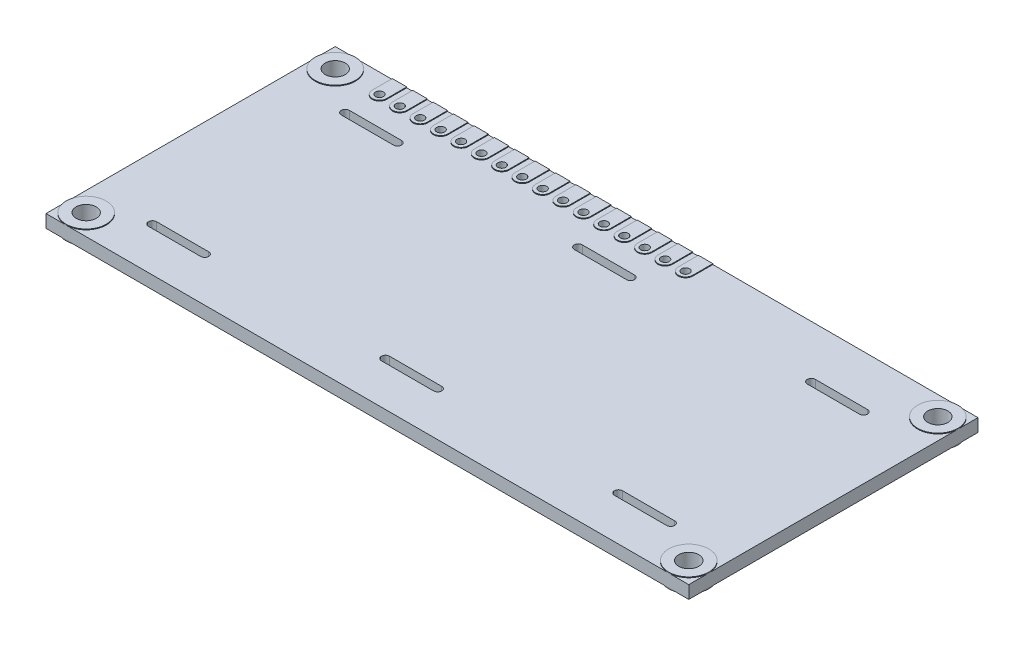
SolidWorks part; units mm, degrees
ref_plane "Front Plane" through (0, 0, 0) normal (0, 0, 1) x (1, 0, 0)
ref_plane "Top Plane" through (0, 0, 0) normal (0, 1, 0) x (1, 0, 0)
ref_plane "Right Plane" through (0, 0, 0) normal (1, 0, 0) x (0, 0, -1)
sketch "Sketch1" plane through (0, 0, 0) normal (0, 1, 0) x (1, 0, 0)
  line L0 (-32, 15.5) -> (-29.46, 15.5) construction
  line L1 (40, 18) -> (-40, 18)
  line L2 (40, 18) -> (40, -18)
  line L3 (40, -18) -> (-40, -18)
  line L4 (-40, 18) -> (-40, -18)
  line L5 (40, 18) -> (-40, -18) construction
  line L6 (40, -18) -> (-40, 18) construction
  line L7 (-37.5, 15.5) -> (37.5, 15.5) construction
  line L8 (-37.5, 15.5) -> (-37.5, -15.5) construction
  line L10 (37.5, 15.5) -> (37.5, -15.5) construction
  line L11 (-37.5, 15.5) -> (37.5, -15.5) construction
  line L12 (-37.5, -15.5) -> (37.5, 15.5) construction
  line L13 (0, 15.5) -> (0, -15.5) construction
  line L14 (-3.25, -12.5) -> (3.25, -12.5) construction
  line L15 (-3.25, -12) -> (3.25, -12)
  line L16 (-3.25, -13) -> (3.25, -13)
  line L17 (25.75, -12.5) -> (32.25, -12.5) construction
  line L18 (25.75, -12) -> (32.25, -12)
  line L19 (25.75, -13) -> (32.25, -13)
  line L20 (25.75, 11.5) -> (32.25, 11.5) construction
  line L21 (25.75, 12) -> (32.25, 12)
  line L22 (25.75, 11) -> (32.25, 11)
  line L23 (-3.25, 11.5) -> (3.25, 11.5) construction
  line L24 (-3.25, 12) -> (3.25, 12)
  line L25 (-3.25, 11) -> (3.25, 11)
  line L26 (-32.25, -12.5) -> (-25.75, -12.5) construction
  line L27 (-32.25, -12) -> (-25.75, -12)
  line L28 (-32.25, -13) -> (-25.75, -13)
  line L29 (-32.25, 11.5) -> (-25.75, 11.5) construction
  line L30 (-32.25, 12) -> (-25.75, 12)
  line L31 (-32.25, 11) -> (-25.75, 11)
  circle A0 centre (-37.5, 15.5) radius 1.25
  circle A1 centre (-37.5, -15.5) radius 1.25
  circle A2 centre (37.5, 15.5) radius 1.25
  circle A3 centre (37.5, -15.5) radius 1.25
  circle A4 centre (-32, 15.5) radius 0.5
  circle A5 centre (-29.46, 15.5) radius 0.5
  circle A6 centre (-26.92, 15.5) radius 0.5
  circle A7 centre (-24.38, 15.5) radius 0.5
  circle A8 centre (-21.84, 15.5) radius 0.5
  circle A9 centre (-19.3, 15.5) radius 0.5
  circle A10 centre (-16.76, 15.5) radius 0.5
  circle A11 centre (-14.22, 15.5) radius 0.5
  circle A12 centre (-11.68, 15.5) radius 0.5
  circle A13 centre (-9.14, 15.5) radius 0.5
  circle A14 centre (-6.6, 15.5) radius 0.5
  circle A15 centre (-4.06, 15.5) radius 0.5
  circle A16 centre (-1.52, 15.5) radius 0.5
  circle A17 centre (1.02, 15.5) radius 0.5
  circle A18 centre (3.56, 15.5) radius 0.5
  circle A19 centre (6.1, 15.5) radius 0.5
  arc A20 (-3.25, -12) -> (-3.25, -13) centre (-3.25, -12.5) ccw
  arc A21 (3.25, -13) -> (3.25, -12) centre (3.25, -12.5) ccw
  arc A22 (25.75, -12) -> (25.75, -13) centre (25.75, -12.5) ccw
  arc A23 (32.25, -13) -> (32.25, -12) centre (32.25, -12.5) ccw
  arc A24 (25.75, 12) -> (25.75, 11) centre (25.75, 11.5) ccw
  arc A25 (32.25, 11) -> (32.25, 12) centre (32.25, 11.5) ccw
  arc A26 (-3.25, 12) -> (-3.25, 11) centre (-3.25, 11.5) ccw
  arc A27 (3.25, 11) -> (3.25, 12) centre (3.25, 11.5) ccw
  arc A28 (-32.25, -12) -> (-32.25, -13) centre (-32.25, -12.5) ccw
  arc A29 (-25.75, -13) -> (-25.75, -12) centre (-25.75, -12.5) ccw
  arc A30 (-32.25, 12) -> (-32.25, 11) centre (-32.25, 11.5) ccw
  arc A31 (-25.75, 11) -> (-25.75, 12) centre (-25.75, 11.5) ccw
  point P0 (0, 0)
  point P6 (0, 0)
  point P51 (-29, 0)
  point P52 (0, -12.5)
  point P55 (0, -12.5)
  point P60 (-29, 0)
  point P62 (29, -12.5)
  point P65 (29, -12.5)
  point P70 (29, 11.5)
  point P73 (29, 11.5)
  point P78 (0, 11.5)
  point P81 (0, 11.5)
  point P86 (-29, -12.5)
  point P89 (-29, -12.5)
  point P94 (-29, 11.5)
  point P97 (-29, 11.5)
  dimension "D5" = 2.5
  dimension "D6" = 1
  dimension "D1" = 36
  dimension "D2" = 80
  dimension "D3" = 2.5
  dimension "D4" = 2.5
  dimension "D7" = 8
  dimension "D9" = 2.54
  dimension "D10" = 1
  dimension "D11" = 6.5
  dimension "D12" = 5
  dimension "D8" = 16
  dimension "D13" = 2
  dimension "D14" = 2
  dimension "D15" = 2
extrude "Boss-Extrude1" add sketch "Sketch1" against normal blind 1.6
sketch "Sketch2" plane through (0, 0, 0) normal (0, 1, 0) x (1, 0, 0)
  line L0 (-32.9, 15.5) -> (-32.9, 18)
  line L1 (40, 18) -> (-40, 18) construction
  line L2 (-32.9, 18) -> (-31.1, 18)
  line L3 (-31.1, 18) -> (-31.1, 15.5)
  arc A0 (-31.1, 15.5) -> (-32.9, 15.5) centre (-32, 15.5) cw
  circle A1 centre (-32, 15.5) radius 0.5 construction
  circle A2 centre (-32, 15.5) radius 0.5
  dimension "D1" = 1.8
extrude "Boss-Extrude2" add sketch "Sketch2" along normal blind 0.1
pattern_linear "LPattern1" count 16 spacing 2.54 along (1, 0, 0) of "Boss-Extrude2"
sketch "Sketch3" plane through (0, 0, 0) normal (0, 1, 0) x (1, 0, 0)
  circle A0 centre (-37.5, 15.5) radius 1.25 construction
  circle A1 centre (-37.5, -15.5) radius 1.25 construction
  circle A2 centre (37.5, 15.5) radius 1.25 construction
  circle A3 centre (37.5, -15.5) radius 1.25 construction
  circle A4 centre (-37.5, 15.5) radius 1.25
  circle A5 centre (-37.5, -15.5) radius 1.25
  circle A6 centre (37.5, 15.5) radius 1.25
  circle A7 centre (37.5, -15.5) radius 1.25
  circle A8 centre (-37.5, 15.5) radius 2.5
  circle A9 centre (-37.5, -15.5) radius 2.5
  circle A10 centre (37.5, -15.5) radius 2.5
  circle A11 centre (37.5, 15.5) radius 2.5
  dimension "D1" = 1.25
extrude "Boss-Extrude3" add sketch "Sketch3" along normal blind 0.1
sketch "Sketch4" plane through (0, -1.6, 0) normal (0, -1, 0) x (1, 0, 0)
  circle A0 centre (37.5, -15.5) radius 1.25 construction
  circle A1 centre (37.5, 15.5) radius 1.25 construction
  circle A2 centre (-37.5, 15.5) radius 1.25 construction
  circle A3 centre (-37.5, -15.5) radius 1.25 construction
  circle A4 centre (37.5, -15.5) radius 1.25
  circle A5 centre (37.5, 15.5) radius 1.25
  circle A6 centre (-37.5, 15.5) radius 1.25
  circle A7 centre (-37.5, -15.5) radius 1.25
  circle A8 centre (37.5, -15.5) radius 2.5
  circle A9 centre (37.5, 15.5) radius 2.5
  circle A10 centre (-37.5, 15.5) radius 2.5
  circle A11 centre (-37.5, -15.5) radius 2.5
  dimension "D1" = 1.25
extrude "Boss-Extrude4" add sketch "Sketch4" along normal blind 0.1
